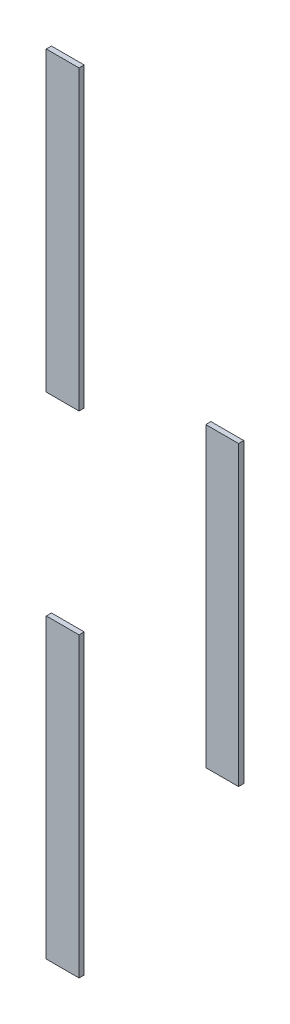
SolidWorks part; units mm, degrees
ref_plane "Front Plane" through (0, 0, 0) normal (0, 0, 1) x (1, 0, 0)
ref_plane "Top Plane" through (0, 0, 0) normal (0, 1, 0) x (1, 0, 0)
ref_plane "Right Plane" through (0, 0, 0) normal (1, 0, 0) x (0, 0, -1)
sketch "Sketch1" plane through (0, 0, 0) normal (0, 0, 1) x (1, 0, 0)
  line L1 (-36.9281, -10) -> (-24.2281, -10)
  line L2 (-36.9281, -10) -> (-36.9281, 105)
  line L3 (-36.9281, 105) -> (-24.2281, 105)
  line L4 (-24.2281, -10) -> (-24.2281, 105)
  line L5 (24.8034, 85) -> (37.5034, 85)
  line L6 (24.8034, 85) -> (24.8034, 200)
  line L7 (24.8034, 200) -> (37.5034, 200)
  line L8 (37.5034, 85) -> (37.5034, 200)
  line L9 (-36.9281, 180) -> (-24.2281, 180)
  line L10 (-36.9281, 180) -> (-36.9281, 295)
  line L11 (-36.9281, 295) -> (-24.2281, 295)
  line L12 (-24.2281, 180) -> (-24.2281, 295)
  dimension "D1" = 10
  dimension "D2" = 10
  dimension "D3" = 12.7
  dimension "D4" = 6.35
  dimension "D5" = 12.7
  dimension "D6" = 10
  dimension "D7" = 6.35
  dimension "D8" = 10
  dimension "D9" = 10
  dimension "D10" = 10
  dimension "D11" = 12.7
  dimension "D12" = 6.35
extrude "Boss-Extrude1" add sketch "Sketch1" along normal blind 2
